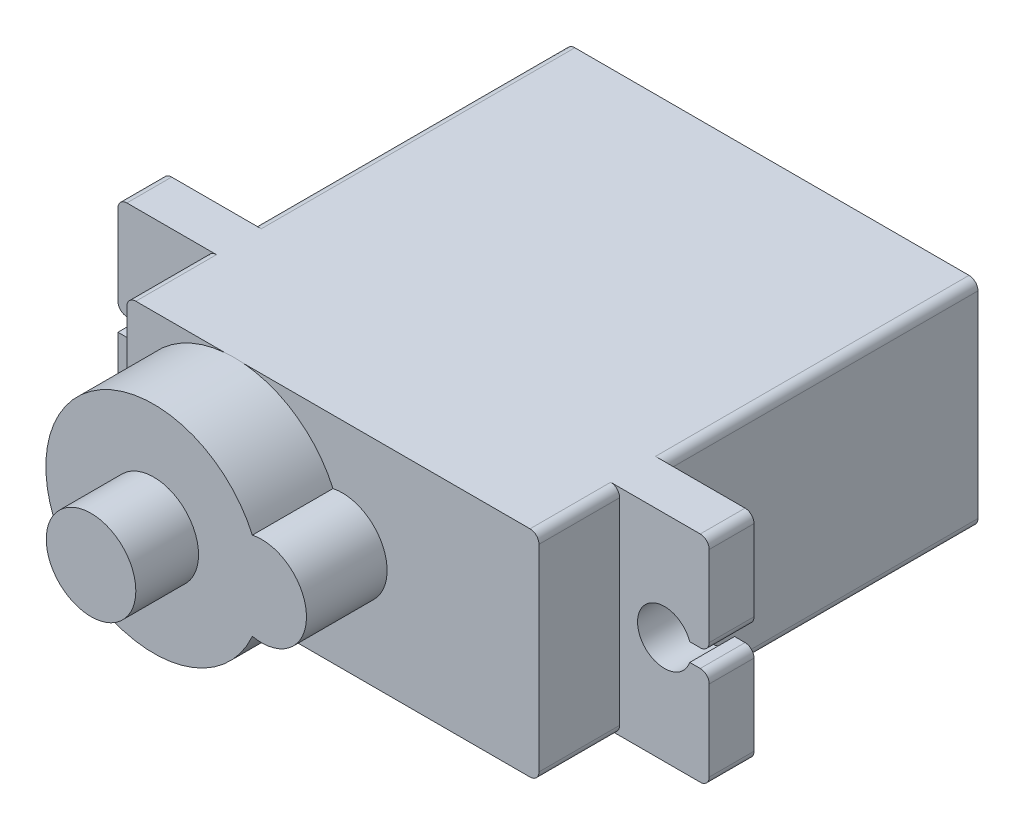
SolidWorks part; units mm, degrees
ref_plane "Plan de face" through (0, 0, 0) normal (0, 0, 1) x (1, 0, 0)
ref_plane "Plan de dessus" through (0, 0, 0) normal (0, 1, 0) x (1, 0, 0)
ref_plane "Plan de droite" through (0, 0, 0) normal (1, 0, 0) x (0, 0, -1)
sketch "Esquisse1" plane through (0, 0, 0) normal (0, 0, 1) x (1, 0, 0)
  line L1 (-16.4106, 10.4126) -> (6.5894, 10.4126)
  line L2 (-16.4106, 10.4126) -> (-16.4106, -1.5874)
  line L3 (-16.4106, -1.5874) -> (6.5894, -1.5874)
  line L4 (6.5894, 10.4126) -> (6.5894, -1.5874)
  dimension "D1" = 23
  dimension "D2" = 12
extrude "Boss.-Extru.1" add sketch "Esquisse1" along normal blind 17.5
sketch "Esquisse2" plane through (0, 0, 17.5) normal (0, 0, 1) x (1, 0, 0)
  line L0 (-16.4106, -1.5874) -> (6.5894, -1.5874) construction
  line L1 (-21.4106, 10.4126) -> (11.5894, 10.4126)
  line L2 (-21.4106, 10.4126) -> (-21.4106, -1.5874)
  line L3 (-21.4106, -1.5874) -> (11.5894, -1.5874)
  line L4 (11.5894, 10.4126) -> (11.5894, -1.5874)
  line L5 (6.5894, 10.4126) -> (-16.4106, 10.4126) construction
  line L6 (-16.4106, 10.4126) -> (-16.4106, -1.5874) construction
  line L8 (6.5894, -1.5874) -> (6.5894, 10.4126) construction
  dimension "D1" = 0
  dimension "D2" = 5
  dimension "D3" = 0
  dimension "D4" = 5
extrude "Boss.-Extru.2" add sketch "Esquisse2" along normal blind 2.5
sketch "Esquisse3" plane through (0, 0, 20) normal (0, 0, 1) x (1, 0, 0)
  line L0 (11.5894, 10.4126) -> (-21.4106, 10.4126) construction
  line L1 (-16.4106, 10.4126) -> (6.5894, 10.4126)
  line L2 (-16.4106, 10.4126) -> (-16.4106, -1.5874)
  line L3 (-16.4106, -1.5874) -> (6.5894, -1.5874)
  line L4 (6.5894, 10.4126) -> (6.5894, -1.5874)
  line L5 (-21.4106, -1.5874) -> (11.5894, -1.5874) construction
  line L6 (-21.4106, 10.4126) -> (-21.4106, -1.5874) construction
  line L7 (11.5894, -1.5874) -> (11.5894, 10.4126) construction
  dimension "D1" = 5
  dimension "D2" = 5
extrude "Boss.-Extru.3" add sketch "Esquisse3" along normal blind 4.5
sketch "Esquisse4" plane through (0, 0, 24.5) normal (0, 0, 1) x (1, 0, 0)
  line L0 (-16.4106, 4.4126) -> (6.5894, 4.4126) construction
  line L1 (-16.4106, 10.4126) -> (-16.4106, -1.5874) construction
  line L2 (6.5894, -1.5874) -> (6.5894, 10.4126) construction
  line L3 (6.5894, 10.4126) -> (-16.4106, 10.4126) construction
  circle A0 centre (-10.4106, 4.4126) radius 6.0226
  dimension "D1" = 6
  dimension "D2" = 6
extrude "Boss.-Extru.4" add sketch "Esquisse4" along normal blind 4.5
sketch "Esquisse5" plane through (0, 0, 24.5) normal (0, 0, 1) x (1, 0, 0)
  line L0 (6.5894, 4.4126) -> (-16.4332, 4.4126) construction
  line L1 (6.5894, -1.5874) -> (6.5894, 10.4126) construction
  circle A0 centre (-10.4106, 4.4126) radius 6.0226 construction
  circle A1 centre (-4.388, 4.4126) radius 2.5
  arc A2 (-9.8894, -1.5874) -> (-9.8894, 10.4126) centre (-10.4106, 4.4126) ccw construction
  dimension "D1" = 5
extrude "Boss.-Extru.5" add sketch "Esquisse5" along normal blind 4.5
sketch "Esquisse6" plane through (0, 0, 29) normal (0, 0, 1) x (1, 0, 0)
  circle A0 centre (-10.4106, 4.4126) radius 2.5
  dimension "D1" = 5
extrude "Boss.-Extru.6" add sketch "Esquisse6" along normal blind 3.5
sketch "Esquisse7" plane through (0, 0, 20) normal (0, 0, 1) x (1, 0, 0)
  line L0 (-21.4106, 4.4126) -> (-16.4106, 4.4126) construction
  line L3 (-21.4106, 10.4126) -> (-21.4106, -1.5874) construction
  line L4 (-16.4106, 10.4126) -> (-16.4106, -1.5874) construction
  line L5 (-16.4106, 4.4126) -> (6.5894, 4.4126) construction
  line L6 (6.5894, -1.5874) -> (6.5894, 10.4126) construction
  line L7 (6.5894, 4.4126) -> (11.5894, 4.4126) construction
  line L8 (11.5894, -1.5874) -> (11.5894, 10.4126) construction
  line L10 (12.6752, 4.9126) -> (10.5036, 4.9126)
  line L11 (12.6752, 4.9126) -> (12.6752, 3.9126)
  line L12 (12.6752, 3.9126) -> (10.5036, 3.9126)
  line L13 (10.5036, 4.9126) -> (10.5036, 3.9126)
  line L14 (12.6752, 4.9126) -> (10.5036, 3.9126) construction
  line L15 (12.6752, 3.9126) -> (10.5036, 4.9126) construction
  line L16 (-22.4964, 3.9126) -> (-20.3248, 3.9126)
  line L17 (-22.4964, 3.9126) -> (-22.4964, 4.9126)
  line L18 (-22.4964, 4.9126) -> (-20.3248, 4.9126)
  line L19 (-20.3248, 3.9126) -> (-20.3248, 4.9126)
  line L20 (-22.4964, 3.9126) -> (-20.3248, 4.9126) construction
  line L21 (-22.4964, 4.9126) -> (-20.3248, 3.9126) construction
  circle A0 centre (-18.9106, 4.4126) radius 1.5
  circle A1 centre (9.0894, 4.4126) radius 1.5
  line M10 (-21.4106, 10.4126) -> (-21.4106, -1.5874)
  dimension "D1" = 3
  dimension "D2" = 3
  dimension "D3" = 1
  dimension "D4" = 1
extrude "Enlèv. mat.-Extru.3" cut sketch "Esquisse7" against normal through all contours L19 A0 | A0 L18 L16 M10 | L13 A1 | A1 L12 L11 L10
fillet "Congé2" radius 0.5 15 edges at (6.5894, 10.4126, 22.25) (6.5894, -1.5874, 22.25) (-16.4106, -1.5874, 22.25) (-16.4106, 10.4126, 22.25) (-21.4106, 10.4126, 18.75) (-21.4106, 4.9126, 18.75) (-21.4106, -1.5874, 18.75) (11.5894, 3.9126, 18.75) (11.5894, 4.9126, 18.75) (11.5894, 10.4126, 18.75) (11.5894, -1.5874, 18.75) (6.5894, -1.5874, 8.75) (-16.4106, -1.5874, 8.75) (6.5894, 10.4126, 8.75) (-16.4106, 10.4126, 8.75)
sketch "Esquisse8" plane through (0, 0, 32.5) normal (0, 0, 1) x (1, 0, 0)
  point P0 (-10.4106, 4.4126)
